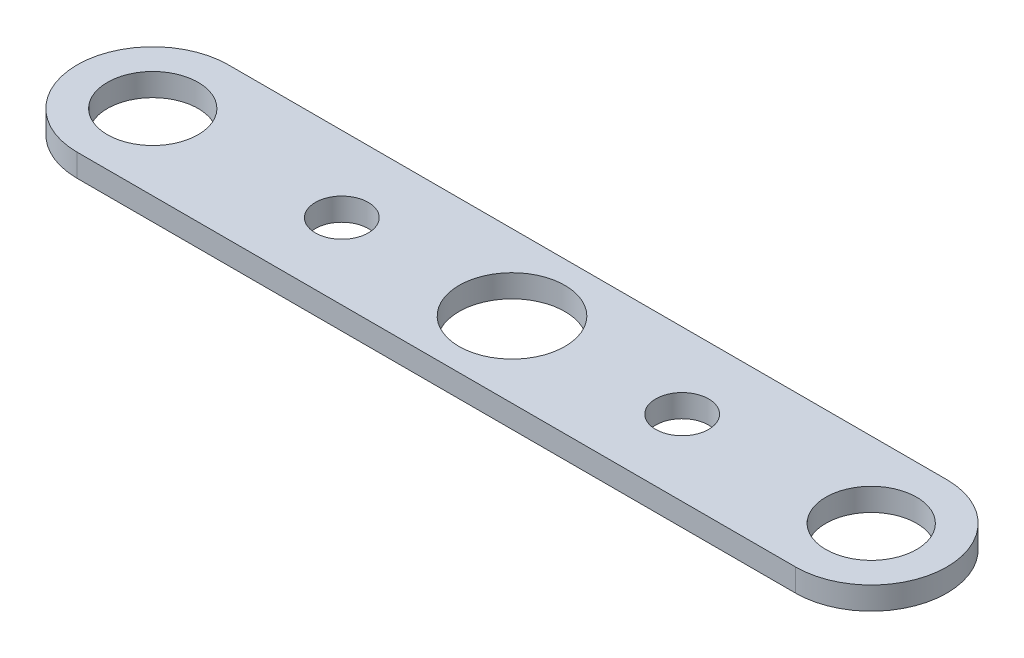
SolidWorks part; units mm, degrees
ref_plane "Front" through (0, 0, 0) normal (0, 0, 1) x (1, 0, 0)
ref_plane "Top" through (0, 0, 0) normal (0, 1, 0) x (1, 0, 0)
ref_plane "Right" through (0, 0, 0) normal (1, 0, 0) x (0, 0, -1)
sketch "Sketch1" plane through (0, 0, 0) normal (0, 1, 0) x (1, 0, 0)
  line L0 (-7.0926, 9.3269) -> (87.9074, 9.3269) construction
  line L1 (-7.0926, 19.3269) -> (87.9074, 19.3269)
  line L2 (-7.0926, -0.6731) -> (87.9074, -0.6731)
  arc A0 (-7.0926, 19.3269) -> (-7.0926, -0.6731) centre (-7.0926, 9.3269) ccw
  arc A1 (87.9074, -0.6731) -> (87.9074, 19.3269) centre (87.9074, 9.3269) ccw
  circle A2 centre (-7.0926, 9.3269) radius 6
  circle A3 centre (87.9074, 9.3269) radius 6
  point P2 (40.4074, 9.3269)
  dimension "D3" = 12
  dimension "D4" = 12
  dimension "D1" = 20
  dimension "D2" = 95
extrude "Boss-Extrude1" add sketch "Sketch1" along normal blind 3
sketch "Sketch2" plane through (0, 3, 0) normal (0, 1, 0) x (1, 0, 0)
  circle A0 centre (40.4074, 9.3269) radius 7
extrude "Cut-Extrude1" cut sketch "Sketch2" against normal through all
sketch "Sketch3" plane through (0, 3, 0) normal (0, 1, 0) x (1, 0, 0)
  circle A0 centre (17.9074, 9.3269) radius 3.5
  circle A1 centre (62.9074, 9.3269) radius 3.5
  circle A2 centre (40.4074, 9.3269) radius 7 construction
  dimension "D1" = 45
  dimension "D2" = 22.5
extrude "Cut-Extrude2" cut sketch "Sketch3" against normal through all
